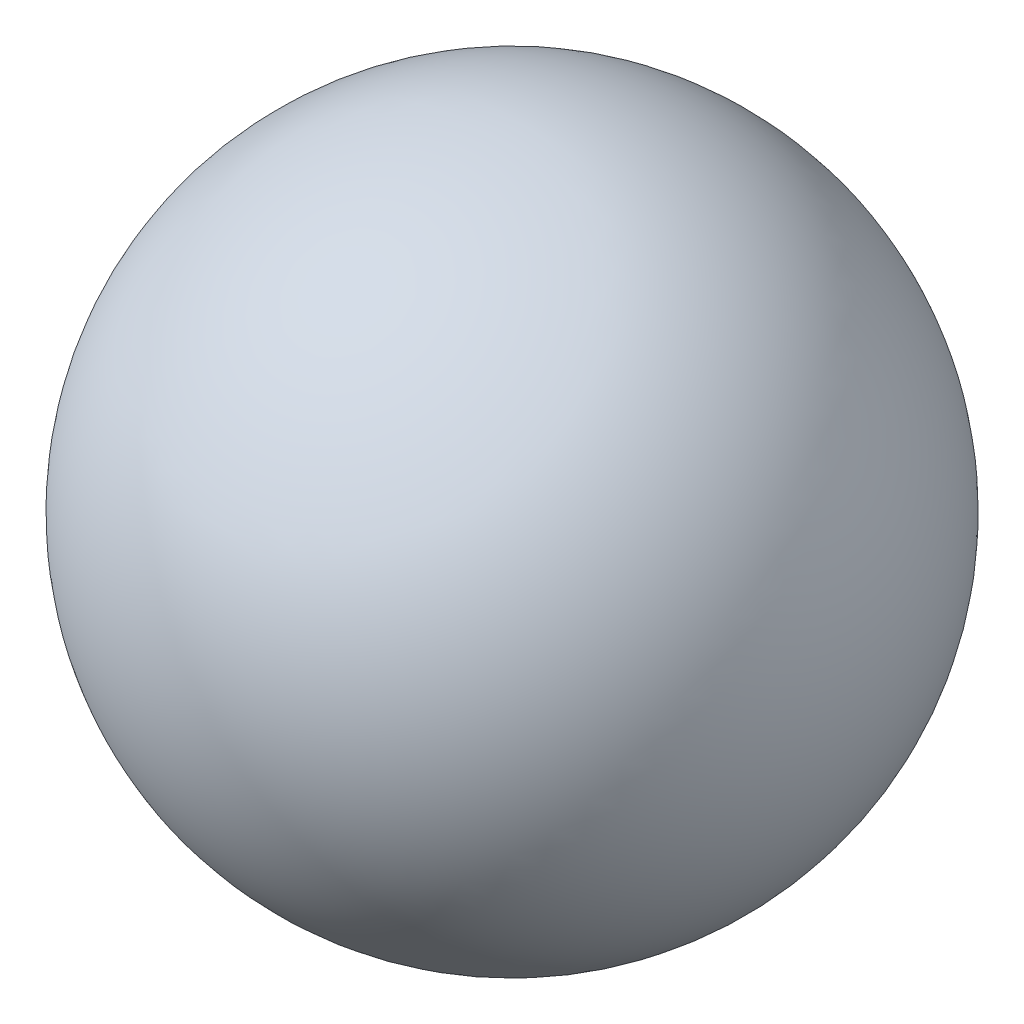
SolidWorks part; units mm, degrees
ref_plane "Front Plane" through (0, 0, 0) normal (0, 0, 1) x (1, 0, 0)
ref_plane "Top Plane" through (0, 0, 0) normal (0, 1, 0) x (1, 0, 0)
ref_plane "Right Plane" through (0, 0, 0) normal (1, 0, 0) x (0, 0, -1)
sketch "Sketch2" plane through (0, 0, 0) normal (0, 1, 0) x (1, 0, 0)
  line L0 (0, -3.8125) -> (0, -3.6618) construction
  line L1 (0, 3.9688) -> (0, -3.9688)
  arc A0 (0, 3.9688) -> (0, -3.9688) centre (0, 0) ccw
  dimension "D1" = 7.9375
revolve "Revolve2" add sketch "Sketch2" angle 360 about L0
